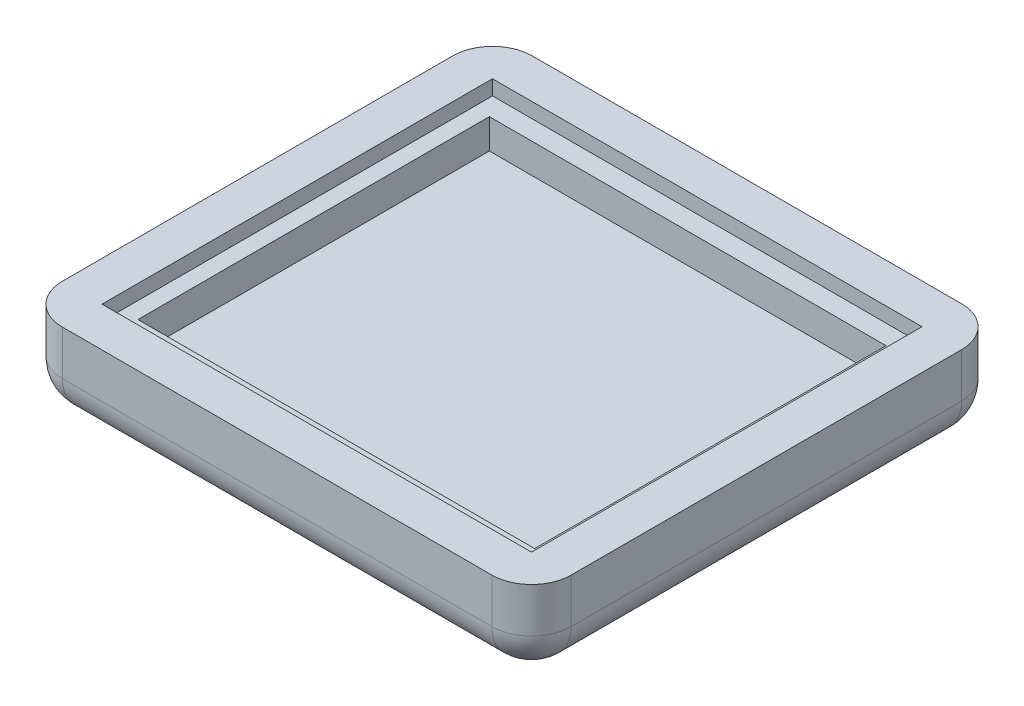
SolidWorks part; units mm, degrees
ref_plane "Front Plane" through (0, 0, 0) normal (0, 0, 1) x (1, 0, 0)
ref_plane "Top Plane" through (0, 0, 0) normal (0, 1, 0) x (1, 0, 0)
ref_plane "Right Plane" through (0, 0, 0) normal (1, 0, 0) x (0, 0, -1)
sketch "Sketch1" plane through (0, 0, 0) normal (0, 1, 0) x (1, 0, 0)
  line L1 (0, 0) -> (55, 0)
  line L2 (0, 0) -> (0, 50)
  line L3 (0, 50) -> (55, 50)
  line L4 (55, 0) -> (55, 50)
  line L5 (0, 0) -> (-5.08, 0)
  line L6 (0, 0) -> (0, -5.08)
  line L7 (0, -5.08) -> (-5.08, -5.08)
  line L8 (-5.08, 0) -> (-5.08, -5.08)
  line L9 (55, 50) -> (60.08, 50)
  line L10 (55, 50) -> (55, 55.08)
  line L11 (55, 55.08) -> (60.08, 55.08)
  line L12 (60.08, 50) -> (60.08, 55.08)
  line L13 (-5.08, -5.08) -> (60.08, -5.08)
  line L14 (-5.08, -5.08) -> (-5.08, 55.08)
  line L15 (-5.08, 55.08) -> (60.08, 55.08)
  line L16 (60.08, -5.08) -> (60.08, 55.08)
  dimension "D1" = 50
  dimension "D2" = 55
  dimension "D3" = 5.08
  dimension "D4" = 5.08
  dimension "D5" = 5.08
  dimension "D6" = 5.08
extrude "Boss-Extrude1" add sketch "Sketch1" against normal blind 5.715 contours L15 L14 L5 L2 L3 L10 | L13 L16 L9 L4 L1 L6 | L5 L8 L7 L6 | L9 L12 L11 L10
sketch "Sketch2" plane through (0, -5.715, 0) normal (0, -1, 0) x (-1, 0, 0)
  line L1 (5.08, 55.08) -> (-60.08, 55.08)
  line L2 (5.08, 55.08) -> (5.08, -5.08)
  line L3 (5.08, -5.08) -> (-60.08, -5.08)
  line L4 (-60.08, 55.08) -> (-60.08, -5.08)
extrude "Boss-Extrude2" add sketch "Sketch2" along normal blind 5.08
fillet "Fillet1" radius 5.08 8 edges at (-5.08, -5.3975, 5.08) (27.5, -10.795, 5.08) (60.08, -5.3975, 5.08) (60.08, -10.795, -25) (60.08, -5.3975, -55.08) (27.5, -10.795, -55.08) (-5.08, -5.3975, -55.08) (-5.08, -10.795, -25)
sketch "Sketch3" plane through (0, -5.715, 0) normal (0, 1, 0) x (1, 0, 0)
  line L1 (55, 50) -> (0, 50)
  line L2 (55, 50) -> (55, 0)
  line L3 (55, 0) -> (0, 0)
  line L4 (0, 50) -> (0, 0)
extrude "Boss-Extrude3" add sketch "Sketch3" along normal blind 3.81
sketch "Sketch4" plane through (0, -1.905, 0) normal (0, 1, 0) x (1, 0, 0)
  line L0 (55, 50) -> (0, 0)
  line L1 (0, 50) -> (55, 0)
  line L3 (2.1, 2.5) -> (52.9, 2.5)
  line L4 (2.1, 2.5) -> (2.1, 47.5)
  line L5 (2.1, 47.5) -> (52.9, 47.5)
  line L6 (52.9, 2.5) -> (52.9, 47.5)
  line L7 (2.1, 2.5) -> (52.9, 47.5) construction
  line L8 (2.1, 47.5) -> (52.9, 2.5) construction
  point P8 (27.5, 25)
  point P13 (27.5, 25)
extrude "Cut-Extrude1" cut sketch "Sketch4" against normal blind 3.81 contours L5 L1 L0 | L3 L6 L5 L0 L1 | L0 L3 L1 | L5 L4 L3 L0 L1
